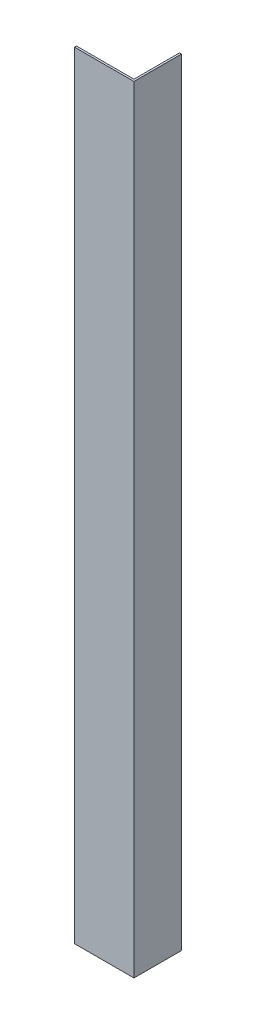
SolidWorks part; units mm, degrees
material "6061-T6 (SS)"
ref_plane "Alzado" through (0, 0, 0) normal (0, 0, 1) x (1, 0, 0)
ref_plane "Planta" through (0, 0, 0) normal (0, 1, 0) x (1, 0, 0)
ref_plane "Vista lateral" through (0, 0, 0) normal (1, 0, 0) x (0, 0, -1)
sketch "Sketch1" plane through (0, 0, 0) normal (0, 1, 0) x (1, 0, 0)
  line L0 (0, 0) -> (15, 0)
  line L1 (15, 0) -> (15, 12)
  line L2 (15, 12) -> (14.5, 12)
  line L3 (14.5, 12) -> (14.5, 0.5)
  line L4 (14.5, 0.5) -> (0, 0.5)
  line L5 (0, 0.5) -> (0, 0)
  dimension "D1" = 15
  dimension "D2" = 12
  dimension "D3" = 0.5
  dimension "D4" = 0.5
extrude "Boss-Extrude1" add sketch "Sketch1" along normal blind 196
sketch "Sketch4" plane through (0, 0, 0) normal (0, 0, 1) x (1, 0, 0)
  line L0 (15, 196) -> (15, 0) construction
  line L1 (0, 196) -> (15, 196)
  line L2 (0, 196) -> (0, 193)
  line L3 (0, 193) -> (15, 193)
  line L4 (15, 196) -> (15, 193)
  line L6 (0, 0) -> (15, 0)
  line L7 (0, 0) -> (0, 3)
  line L8 (0, 3) -> (15, 3)
  line L9 (15, 0) -> (15, 3)
  dimension "D1" = 3
  dimension "D2" = 3
extrude "Cut-Extrude3" [suppressed] cut sketch "Sketch4" against normal up to next
